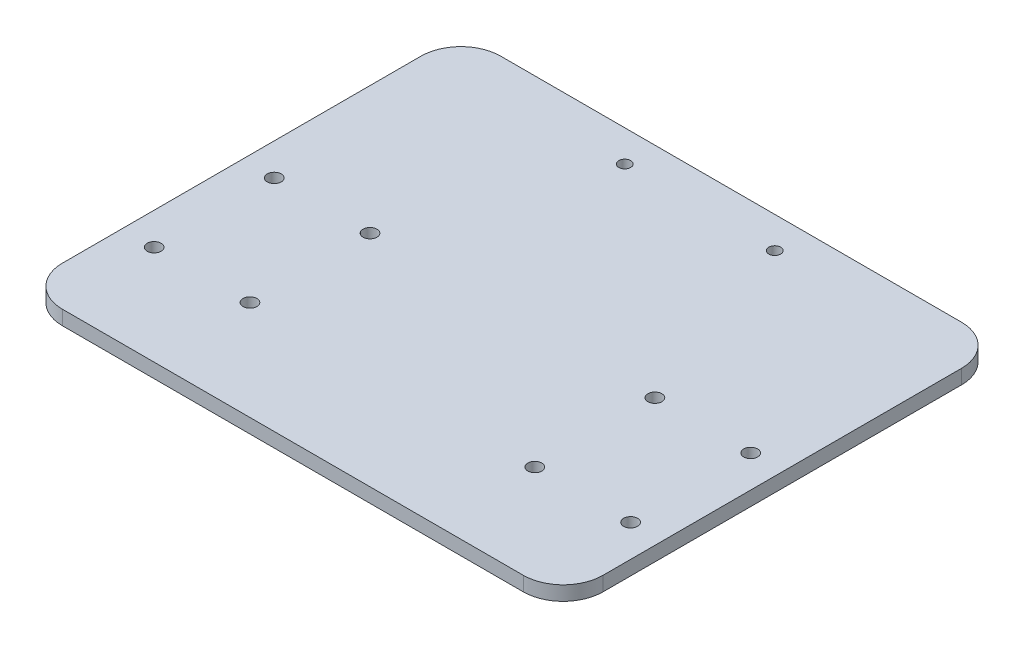
SolidWorks part; units mm, degrees
ref_plane "前视基准面" through (0, 0, 0) normal (0, 0, 1) x (1, 0, 0)
ref_plane "上视基准面" through (0, 0, 0) normal (0, 1, 0) x (1, 0, 0)
ref_plane "右视基准面" through (0, 0, 0) normal (1, 0, 0) x (0, 0, -1)
sketch "草图6" plane through (0, 0, 0) normal (0, 1, 0) x (1, 0, 0)
  line L0 (0, 0) -> (0, 140)
  line L1 (0, 0) -> (190, 0)
  line L2 (0, 140) -> (0, 0)
  line L3 (0, 140) -> (190, 140)
  line L4 (0, 0) -> (190, 0)
  line L5 (190, 140) -> (190, 0)
  line L6 (0, 70) -> (190, 70) construction
  line L7 (95, 0) -> (95, 140) construction
  line L9 (27.2363, 110) -> (162.7637, 110)
  line L10 (27.2363, 110) -> (27.2363, 30)
  line L11 (27.2363, 30) -> (162.7637, 30)
  line L12 (162.7637, 110) -> (162.7637, 30)
  line L13 (95, 30) -> (95, 110) construction
  line L14 (27.2363, 70) -> (162.7637, 70) construction
  line L15 (27.2363, 90) -> (27.2363, 50)
  line L16 (27.2363, 90) -> (67.2363, 90)
  line L17 (27.2363, 50) -> (67.2363, 50)
  line L18 (67.2363, 90) -> (67.2363, 50)
  line L19 (27.2363, 70) -> (67.2363, 70) construction
  line L20 (47.2363, 90) -> (47.2363, 50) construction
  line L21 (59.9899, 86.8) -> (27.9399, 86.8) construction
  line L22 (162.7637, 50) -> (122.7637, 50)
  line L23 (122.7637, 90) -> (122.7637, 50)
  line L24 (162.7637, 90) -> (122.7637, 90)
  line L25 (162.7637, 90) -> (162.7637, 50)
  line L26 (27.2363, 110) -> (162.7637, 110)
  line L27 (27.2363, 110) -> (27.2363, 139.8753)
  line L28 (162.7637, 110) -> (162.7637, 139.8753)
  line L29 (27.2363, 139.8753) -> (162.7637, 139.8753)
  line L30 (95, 132) -> (63.2188, 132) construction
  line L31 (77.7, 132) -> (112.3, 132)
  circle A0 centre (59.2863, 85.05) radius 1.75
  circle A1 centre (35.2863, 85.05) radius 1.75
  circle A2 centre (59.2863, 54.95) radius 1.75
  circle A3 centre (35.2863, 54.95) radius 1.75
  circle A4 centre (130.7137, 54.95) radius 1.75
  circle A5 centre (154.7137, 54.95) radius 1.75
  circle A6 centre (130.7137, 85.05) radius 1.75
  circle A7 centre (154.7137, 85.05) radius 1.75
  circle A8 centre (76.2, 132) radius 1.5
  circle A9 centre (113.8, 132) radius 1.5
  point P12 (95, 70)
  point P17 (95, 70)
  point P21 (61.0363, 85.05)
  point P22 (59.2863, 86.8)
  point P29 (59.2863, 86.8)
  point P30 (37.0363, 85.05)
  point P32 (57.5363, 85.05)
  point P56 (95, 132)
  dimension "D1" = 6.2
  dimension "D3" = 3.5
  dimension "D5" = 140
  dimension "D7" = 8
  dimension "D2" = 3.2
  dimension "D4" = 20.5
  dimension "D6" = 190
  dimension "D8" = 34.6
extrude "凸台-拉伸2" add sketch "草图6" along normal blind 3.6
fillet "圆角1" radius 10 1 edges at (27.2363, 1.8, -30)
fillet "圆角2" radius 10 1 edges at (27.2363, 1.8, -139.8753)
fillet "圆角3" radius 10 1 edges at (162.7637, 1.8, -139.8753)
fillet "圆角4" radius 10 1 edges at (162.7637, 1.8, -30)
